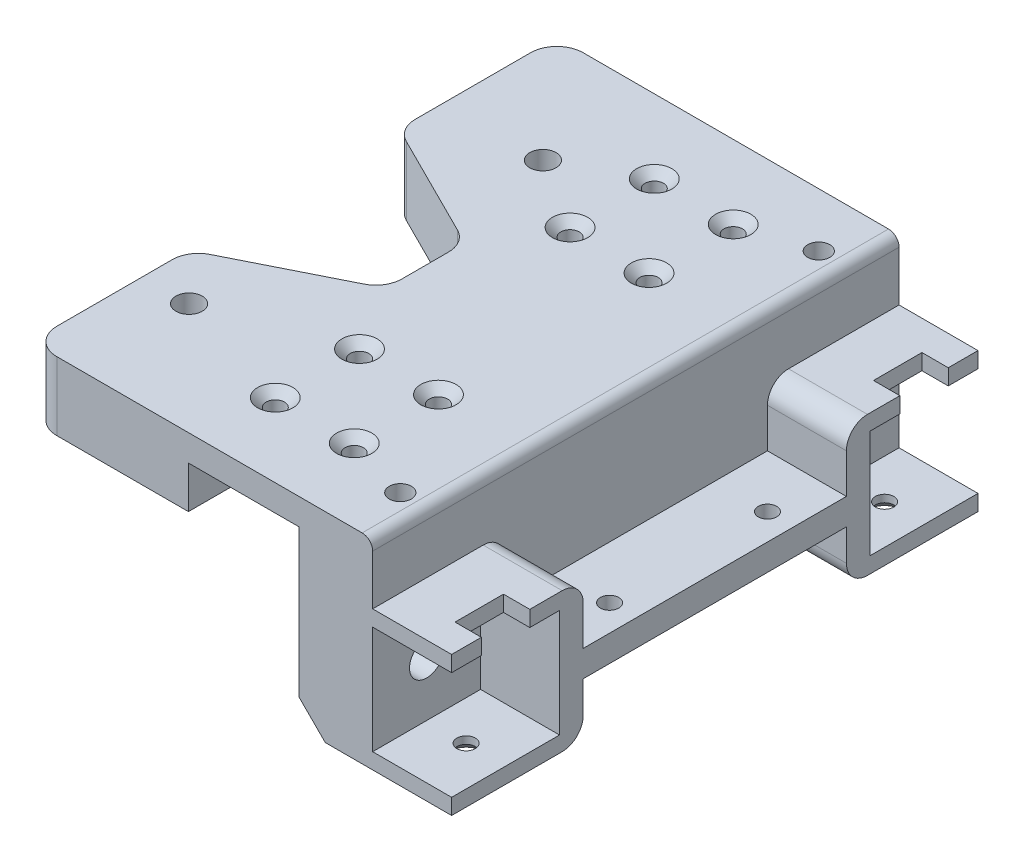
SolidWorks part; units mm, degrees
ref_plane "Front Plane" through (0, 0, 0) normal (0, 0, 1) x (1, 0, 0)
ref_plane "Top Plane" through (0, 0, 0) normal (0, 1, 0) x (1, 0, 0)
ref_plane "Right Plane" through (0, 0, 0) normal (1, 0, 0) x (0, 0, -1)
sketch "Sketch1" plane through (0, 0, 0) normal (0, 1, 0) x (1, 0, 0)
  line L0 (0, 50) -> (0, -50) construction
  line L1 (-10, 50) -> (10, 50)
  line L2 (-10, 50) -> (-10, -50)
  line L3 (-10, -50) -> (10, -50)
  line L4 (10, 50) -> (10, -50) construction
  line L5 (-10, 50) -> (10, -50) construction
  line L6 (-10, -50) -> (10, 50) construction
  line L7 (-7.5, 36) -> (7.5, 36) construction
  line L8 (-7.5, 36) -> (7.5, 20) construction
  line L9 (-10, 0) -> (10, 0) construction
  line L10 (-7.5, -36) -> (7.5, -20) construction
  line L11 (-7.5, -36) -> (7.5, -36) construction
  line L12 (-7.5, 20) -> (7.5, 20) construction
  line L13 (10, 50) -> (11, 50)
  line L14 (11, 50) -> (11, -50)
  line L15 (11, -50) -> (10, -50)
  circle A0 centre (-7.5, 36) radius 1.75
  circle A1 centre (7.5, 36) radius 1.75
  circle A2 centre (-7.5, 20) radius 1.75
  circle A3 centre (7.5, 20) radius 1.75
  circle A4 centre (7.5, -20) radius 1.75
  circle A5 centre (-7.5, -20) radius 1.75
  circle A6 centre (7.5, -36) radius 1.75
  circle A7 centre (-7.5, -36) radius 1.75
  point P0 (0, 0)
  point P16 (0, 36)
  dimension "D2" = 3.5
  dimension "D1" = 20
  dimension "D3" = 15
  dimension "D4" = 16
  dimension "D5" = 100
  dimension "D6" = 20
  dimension "D7" = 1
extrude "Boss-Extrude1" add sketch "Sketch1" along normal blind 5
sketch "Sketch2" plane through (11, 0, 0) normal (1, 0, 0) x (0, 0, -1)
  line L1 (-50, 5) -> (50, 5)
  line L2 (-50, 5) -> (-50, -33)
  line L3 (-50, -33) -> (50, -33)
  line L5 (50, 5) -> (50, -33)
  line L6 (50, 5) -> (50, 0) construction
  line L7 (-50, 5) -> (-50, 0) construction
  line L8 (-50, 5) -> (50, 5) construction
  dimension "D1" = 38
extrude "Boss-Extrude2" add sketch "Sketch2" along normal blind 14
sketch "Sketch3" plane through (25, 0, 0) normal (1, 0, 0) x (0, 0, -1)
  line L0 (0, 5) -> (0, -33) construction
  line L1 (-25, -18) -> (25, -18)
  line L2 (-25, -18) -> (-25, -23)
  line L3 (-25, -23) -> (25, -23)
  line L4 (25, -18) -> (25, -23)
  line L5 (50, 5) -> (-50, 5) construction
  line L6 (-50, -33) -> (50, -33) construction
  point P10 (0, -18)
  dimension "D1" = 5
  dimension "D2" = 50
  dimension "D3" = 10
extrude "Boss-Extrude3" add sketch "Sketch3" along normal blind 15
sketch "Sketch4" plane through (0, -18, 0) normal (0, 1, 0) x (1, 0, 0)
  line L0 (30, 0) -> (40, 0) construction
  line L2 (40, 25) -> (40, -25) construction
  line L3 (35, -15) -> (35, 15) construction
  circle A0 centre (35, 15) radius 1.75
  circle A1 centre (35, -15) radius 1.75
  point P8 (35, 0)
  dimension "D1" = 30
  dimension "D2" = 3.5
  dimension "D3" = 10
extrude "Cut-Extrude1" cut sketch "Sketch4" against normal through all
sketch "Sketch8" plane through (25, 0, 0) normal (1, 0, 0) x (0, 0, -1)
  line L0 (-50, 5) -> (-50, -33) construction
  line L1 (-50, -6.5) -> (-25, -6.5)
  line L2 (-50, -6.5) -> (-50, -9.5)
  line L3 (-50, -33) -> (-25, -33)
  line L4 (-25, -6.5) -> (-25, -33)
  line L5 (-50, -30) -> (-50, -33)
  line L6 (-50, -30) -> (-29.5, -30)
  line L8 (-50, -9.5) -> (-29.5, -9.5)
  line L9 (-29.5, -30) -> (-29.5, -9.5)
  line L10 (0, 20.9) -> (0, -20.9) construction
  line L11 (29.5, -30) -> (29.5, -9.5)
  line L12 (50, -9.5) -> (29.5, -9.5)
  line L13 (50, -30) -> (29.5, -30)
  line L14 (50, -30) -> (50, -33)
  line L15 (25, -6.5) -> (25, -33)
  line L16 (50, -33) -> (25, -33)
  line L17 (50, -6.5) -> (50, -9.5)
  line L18 (50, -6.5) -> (25, -6.5)
  line L19 (-50, -33) -> (50, -33) construction
  line L20 (-25, -18) -> (-25, -23) construction
  dimension "D1" = 3
  dimension "D3" = 3
  dimension "D4" = 20.5
  dimension "D5" = 20.5
extrude "Boss-Extrude6" add sketch "Sketch8" along normal blind 15
sketch "Sketch9" plane through (25, 0, 0) normal (1, 0, 0) x (0, 0, -1)
  line L0 (-50, -9.5) -> (-29.5, -30) construction
  line L1 (50, -9.5) -> (29.5, -30) construction
  circle A0 centre (-39.75, -19.75) radius 3.25
  circle A1 centre (39.75, -19.75) radius 3.25
  dimension "D1" = 6.5
extrude "Cut-Extrude3" cut sketch "Sketch9" against normal through all
sketch "Sketch10" plane through (11, 0, 0) normal (-1, 0, 0) x (0, 0, 1)
  circle A0 centre (-39.75, -19.75) radius 5.25
  circle A1 centre (39.75, -19.75) radius 5.25
  dimension "D1" = 10.5
extrude "Cut-Extrude4" cut sketch "Sketch10" against normal offset from surface (9 mm away) 5 up to face at (25, -19.75, 36.5)
sketch "Sketch11" plane through (0, -6.5, 0) normal (0, 1, 0) x (1, 0, 0)
  line L0 (40, -25) -> (40, -50) construction
  line L1 (40, -35.15) -> (35, -35.15)
  line L2 (40, -35.15) -> (40, -44.35)
  line L3 (40, -44.35) -> (35, -44.35)
  line L4 (35, -35.15) -> (35, -44.35)
  line L5 (35, -39.75) -> (40, -39.75) construction
  line L7 (-10, 0) -> (40, 0) construction
  line L8 (-10, 50) -> (-10, -50) construction
  line L9 (40, 25) -> (40, -25) construction
  line L10 (40, -35.15) -> (35, -35.15)
  line L11 (40, -44.35) -> (35, -44.35)
  line L12 (35, 39.75) -> (40, 39.75) construction
  line L13 (40, 44.35) -> (35, 44.35)
  line L14 (40, 35.15) -> (35, 35.15)
  line L15 (35, 35.15) -> (35, 44.35)
  line L16 (40, 44.35) -> (35, 44.35)
  line L17 (40, 35.15) -> (40, 44.35)
  line L18 (40, 35.15) -> (35, 35.15)
  line L19 (40, -50) -> (40, -29.5) construction
  point P22 (40, -39.75)
  line M7 (40, -50) -> (40, -25)
  dimension "D1" = 9.2
  dimension "D3" = 5
extrude "Cut-Extrude5" cut sketch "Sketch11" against normal up to next contours L1 L4 L3 M7 | L14 L17 L13 L15
sketch "Sketch12" plane through (0, -30, 0) normal (0, 1, 0) x (1, 0, 0)
  line L0 (40, -39.75) -> (25, -39.75) construction
  line L1 (40, -29.5) -> (40, -50) construction
  line L2 (25, -25) -> (25, -50) construction
  line L3 (-20.9, 0) -> (20.9, 0) construction
  circle A0 centre (32.5, -39.75) radius 1.75
  circle A2 centre (32.5, 39.75) radius 1.75
  dimension "D1" = 3.5
extrude "Cut-Extrude6" cut sketch "Sketch12" against normal through all
sketch "Sketch13" plane through (-10, 0, 0) normal (-1, 0, 0) x (0, 0, 1)
  line L1 (-50, 5) -> (50, 5)
  line L2 (-50, 5) -> (-50, -8)
  line L3 (-50, -8) -> (50, -8)
  line L4 (50, 5) -> (50, -8)
  dimension "D1" = 13
extrude "Boss-Extrude7" add sketch "Sketch13" along normal blind 30
sketch "Sketch14" plane through (0, 5, 0) normal (0, 1, 0) x (1, 0, 0)
  line L0 (-40, -50) -> (25, -50) construction
  line L1 (-10.5, -50) -> (10.5, -50) construction
  line L2 (-10.5, -50) -> (-10.5, 50) construction
  line L3 (-10.5, 50) -> (10.5, 50) construction
  line L4 (10.5, -50) -> (10.5, 50) construction
  line L5 (25, 50) -> (-40, 50) construction
  line L6 (0, -35.15) -> (0, 35.15) construction
  line L7 (-37.5775, 50) -> (-37.5775, -50) construction
  line L12 (-31.1525, -35.15) -> (40, -35.15) construction
  line L18 (-21.15, 35.15) -> (40, 35.15) construction
  circle A0 centre (-21.15, 28.4925) radius 2.5
  circle A1 centre (-31.1525, -28.725) radius 2.5
  circle A2 centre (-31.1525, -28.725) radius 6.425 construction
  circle A3 centre (-21.15, 28.4925) radius 6.6575 construction
  circle A4 centre (-30.92, -28.725) radius 6.6575 construction
  point P14 (0, 50)
  point P20 (0, 0)
  dimension "D1" = 5
  dimension "D2" = 5
  dimension "D4" = 21
  dimension "D5" = 12.85
  dimension "D6" = 13.315
  dimension "D8" = 13.315
  dimension "D3" = 21.15
  dimension "D7" = 30.92
extrude "Cut-Extrude7" cut sketch "Sketch14" against normal through all
sketch "Sketch15" plane through (0, -8, 0) normal (0, -1, 0) x (1, 0, 0)
  line L0 (-40, -50) -> (-40, 50) construction
  line L1 (-27.1525, 26.4156) -> (-27.1525, 31.0344)
  line L2 (-27.1525, 31.0344) -> (-31.1525, 33.3438)
  line L3 (-31.1525, 33.3438) -> (-35.1525, 31.0344)
  line L4 (-35.1525, 31.0344) -> (-35.1525, 26.4156)
  line L5 (-35.1525, 26.4156) -> (-31.1525, 24.1062)
  line L6 (-31.1525, 24.1062) -> (-27.1525, 26.4156)
  line L7 (-25.15, -30.8019) -> (-21.15, -33.1113)
  line L8 (-21.15, -33.1113) -> (-17.15, -30.8019)
  line L9 (-17.15, -30.8019) -> (-17.15, -26.1831)
  line L10 (-17.15, -26.1831) -> (-21.15, -23.8737)
  line L11 (-21.15, -23.8737) -> (-25.15, -26.1831)
  line L12 (-25.15, -26.1831) -> (-25.15, -30.8019)
  circle A0 centre (-31.1525, 28.725) radius 4 construction
  circle A1 centre (-21.15, -28.4925) radius 4 construction
  dimension "D1" = 8
extrude "Cut-Extrude8" cut sketch "Sketch15" against normal blind 4
sketch "Sketch16" plane through (0, 5, 0) normal (0, 1, 0) x (1, 0, 0)
  line L0 (20, 39.75) -> (40, 39.75) construction
  line L1 (40, 50) -> (40, 29.5) construction
  line L2 (20, -39.75) -> (40, -39.75) construction
  line L3 (40, -29.5) -> (40, -50) construction
  circle A0 centre (20, 39.75) radius 2.1
  circle A1 centre (20, -39.75) radius 2.1
  dimension "D1" = 4.2
  dimension "D2" = 4.2
  dimension "D3" = 20
extrude "Cut-Extrude9" cut sketch "Sketch16" against normal blind 4
chamfer "Chamfer1" distance 1.6 angle 45 8 edges at (-7.5, 5, -34.25) (7.5, 5, -34.25) (-7.5, 5, -18.25) (7.5, 5, -18.25) (-7.5, 5, 18.25) (7.5, 5, 18.25) (-7.5, 5, 34.25) (7.5, 5, 34.25)
sketch "Sketch17" plane through (0, 5, 0) normal (0, 1, 0) x (1, 0, 0)
  line L0 (-40, 20) -> (-15, 7.5)
  line L1 (-40, -50) -> (-40, 50) construction
  line L2 (-15, 7.5) -> (-15, -7.5)
  line L3 (-15, -7.5) -> (-40, -20)
  line L4 (-40, -20) -> (-40, 20)
  point P6 (-15, 0)
  dimension "D1" = 15
  dimension "D2" = 40
  dimension "D3" = 15
extrude "Cut-Extrude10" cut sketch "Sketch17" against normal through all
chamfer "Chamfer2" distance 1.6 angle 45 2 edges at (32.5, -33, -41.5) (32.5, -33, 41.5)
chamfer "Chamfer3" distance 5 angle 45 1 edges at (11, -33, 0)
sketch "Sketch18" plane through (0, 1, 0) normal (0, 1, 0) x (1, 0, 0)
  circle A0 centre (20, 39.75) radius 1.75
  circle A1 centre (20, -39.75) radius 1.75
  dimension "D1" = 3.5
  dimension "D2" = 3.5
extrude "Cut-Extrude11" cut sketch "Sketch18" against normal blind 4
fillet "Fillet1" radius 5 6 edges at (-40, -1.5, -50) (-40, -1.5, 50) (-40, -1.5, 20) (-15, -1.5, 7.5) (-15, -1.5, -7.5) (-40, -1.5, -20)
fillet "Fillet2" radius 2 1 edges at (25, 5, 0)
fillet "Fillet3" radius 4 4 edges at (32.5, -33, -25) (32.5, -6.5, -25) (32.5, -6.5, 25) (32.5, -33, 25)
